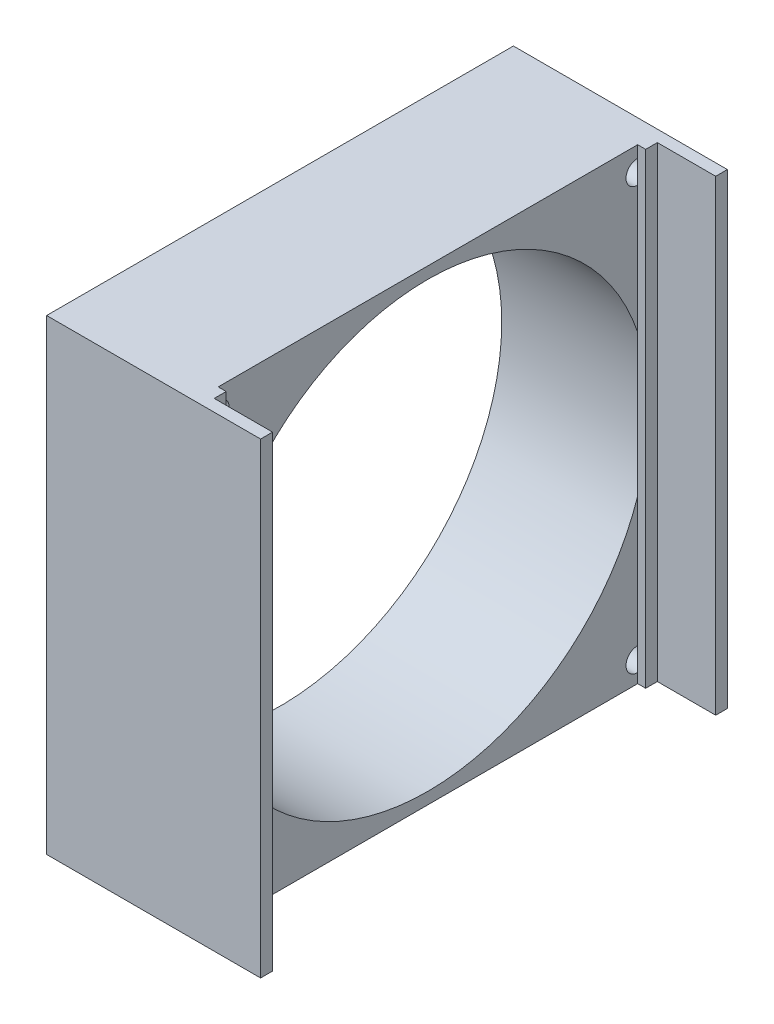
SolidWorks part; units mm, degrees
ref_plane "Front Plane" through (0, 0, 0) normal (0, 0, 1) x (1, 0, 0)
ref_plane "Top Plane" through (0, 0, 0) normal (0, 1, 0) x (1, 0, 0)
ref_plane "Right Plane" through (0, 0, 0) normal (1, 0, 0) x (0, 0, -1)
sketch "Sketch1" plane through (0, 0, 0) normal (1, 0, 0) x (0, 0, -1)
  line L1 (-37.9183, 23.0569) -> (42.0817, 23.0569)
  line L2 (-37.9183, 23.0569) -> (-37.9183, -56.9431)
  line L3 (-37.9183, -56.9431) -> (42.0817, -56.9431)
  line L4 (42.0817, 23.0569) -> (42.0817, -56.9431)
  dimension "D1" = 80
  dimension "D2" = 80
extrude "Boss-Extrude1" add sketch "Sketch1" along normal blind 25.3
sketch "Sketch2" plane through (25.3, 0, 0) normal (1, 0, 0) x (0, 0, -1)
  circle A0 centre (2.0817, -16.9431) radius 38
extrude "Cut-Extrude1" cut sketch "Sketch2" against normal blind 25.3
sketch "Sketch4" plane through (0, 0, 0) normal (-1, 0, 0) x (0, 0, 1)
  line L0 (-42.0817, -56.9431) -> (-42.0817, 23.0569) construction
  line L1 (-42.0817, 23.0569) -> (37.9183, 23.0569) construction
  circle A0 centre (-38.0817, 19.0569) radius 2
  dimension "D1" = 4
  dimension "D2" = 4
extrude "Cut-Extrude2" cut sketch "Sketch4" against normal blind 25.3
sketch "Sketch9" plane through (0, 0, 0) normal (-1, 0, 0) x (0, 0, 1)
  line L0 (37.9183, 23.0569) -> (37.9183, -56.9431) construction
  line L1 (-42.0817, 23.0569) -> (37.9183, 23.0569) construction
  line L2 (37.9183, -56.9431) -> (-42.0817, -56.9431) construction
  line L3 (-42.0817, -56.9431) -> (-42.0817, 23.0569) construction
  circle A0 centre (33.9183, 19.0569) radius 2
  circle A1 centre (33.9183, -52.9431) radius 2
  circle A2 centre (-38.0817, -53.2831) radius 2
  dimension "D1" = 4
  dimension "D2" = 4
  dimension "D3" = 4
  dimension "D4" = 4
  dimension "D5" = 3.6599
  dimension "D6" = 4
extrude "Cut-Extrude3" cut sketch "Sketch9" against normal blind 25.3
sketch "Sketch10" plane through (25.3, 0, 0) normal (1, 0, 0) x (0, 0, -1)
  line L0 (-37.9183, -56.9431) -> (42.0817, -56.9431) construction
  line L1 (-37.9183, 23.0569) -> (-33.8144, 23.0569)
  line L2 (-37.9183, 23.0569) -> (-37.9183, -56.9431)
  line L3 (-37.9183, -56.9431) -> (-33.8144, -56.9431)
  line L4 (-33.8144, 23.0569) -> (-33.8144, -56.9431)
  line L6 (42.0817, 23.0569) -> (38.0817, 23.0569)
  line L7 (42.0817, 23.0569) -> (42.0817, -56.9431)
  line L8 (42.0817, -56.9431) -> (38.0817, -56.9431)
  line L9 (38.0817, 23.0569) -> (38.0817, -56.9431)
extrude "Boss-Extrude2" add sketch "Sketch10" along normal blind 1.37
sketch "Sketch11" plane through (26.67, 0, 0) normal (1, 0, 0) x (0, 0, -1)
  line L0 (-37.9183, -56.9431) -> (-33.8144, -56.9431) construction
  line L1 (-35.8664, -56.9431) -> (-37.9183, -56.9431)
  line L2 (-35.8664, -56.9431) -> (-35.8664, 23.0569)
  line L3 (-35.8664, 23.0569) -> (-37.9183, 23.0569)
  line L4 (-37.9183, -56.9431) -> (-37.9183, 23.0569)
extrude "Boss-Extrude3" add sketch "Sketch11" along normal blind 10
sketch "Sketch12" plane through (26.67, 0, 0) normal (1, 0, 0) x (0, 0, -1)
  line L0 (42.0817, 23.0569) -> (38.0817, 23.0569) construction
  line L1 (42.0817, -56.9431) -> (40.0817, -56.9431)
  line L2 (42.0817, -56.9431) -> (42.0817, 23.0569)
  line L3 (42.0817, 23.0569) -> (40.0817, 23.0569)
  line L4 (40.0817, -56.9431) -> (40.0817, 23.0569)
extrude "Boss-Extrude4" add sketch "Sketch12" along normal blind 10
